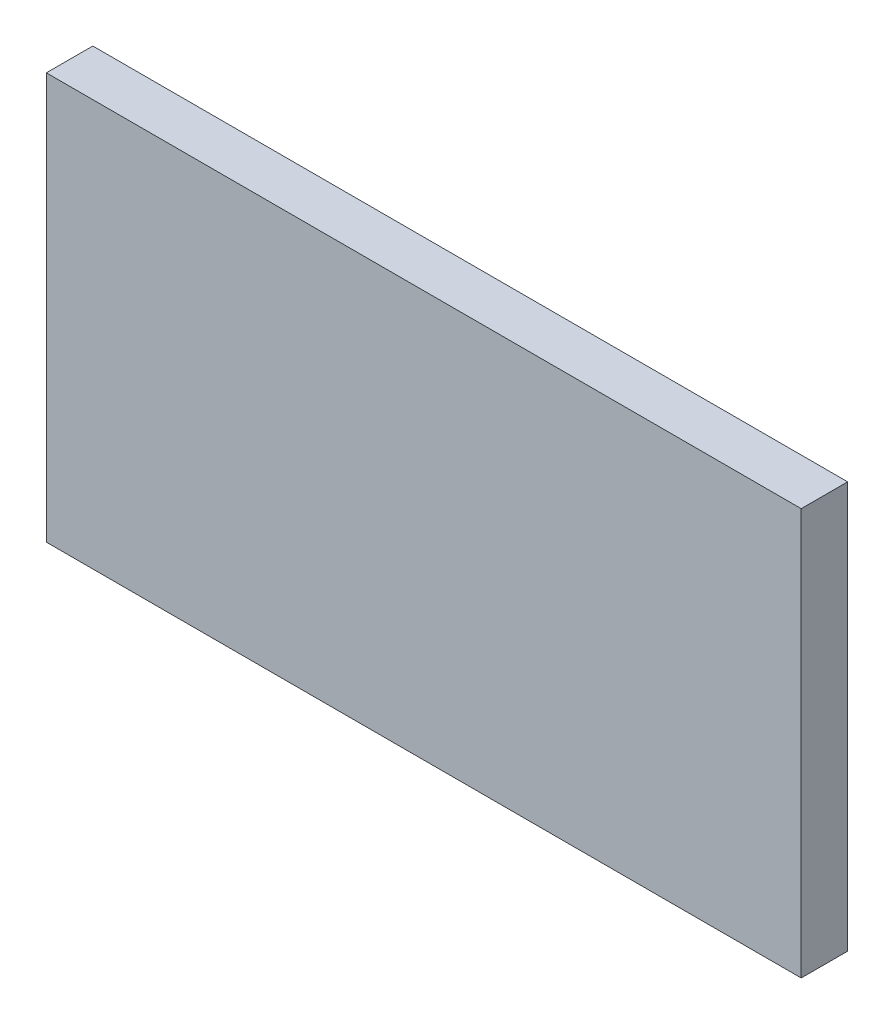
SolidWorks part; units mm, degrees
ref_plane "Front Plane" through (0, 0, 0) normal (0, 0, 1) x (1, 0, 0)
ref_plane "Top Plane" through (0, 0, 0) normal (0, 1, 0) x (1, 0, 0)
ref_plane "Right Plane" through (0, 0, 0) normal (1, 0, 0) x (0, 0, -1)
sketch "Sketch1" plane through (0, 0, 0) normal (0, 0, 1) x (1, 0, 0)
  line L1 (65, 35) -> (-65, 35)
  line L2 (65, 35) -> (65, -35)
  line L3 (65, -35) -> (-65, -35)
  line L4 (-65, 35) -> (-65, -35)
  line L5 (65, 35) -> (-65, -35) construction
  line L6 (65, -35) -> (-65, 35) construction
  point P0 (0, 0)
  dimension "D1" = 70
  dimension "D2" = 130
extrude "Boss-Extrude1" add sketch "Sketch1" along normal blind 8
